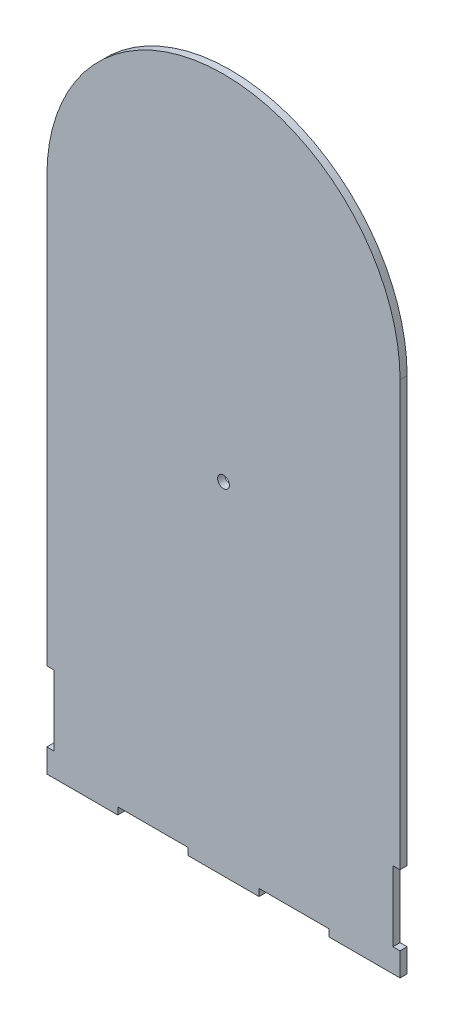
SolidWorks part; units mm, degrees
ref_plane "Front Plane" through (0, 0, 0) normal (0, 0, 1) x (1, 0, 0)
ref_plane "Top Plane" through (0, 0, 0) normal (0, 1, 0) x (1, 0, 0)
ref_plane "Right Plane" through (0, 0, 0) normal (1, 0, 0) x (0, 0, -1)
sketch "Sketch1" plane through (0, 0, 0) normal (0, 0, 1) x (1, 0, 0)
  line L0 (90.1, 0) -> (90.1, 3)
  line L1 (0, 0) -> (150, 0)
  line L2 (0, 0) -> (0, 220)
  line L3 (0, 220) -> (150, 220)
  line L4 (150, 0) -> (150, 220)
  line L5 (150, 39.8) -> (147, 39.8)
  line L6 (150, 39.8) -> (150, 10)
  line L7 (150, 10) -> (147, 10)
  line L8 (147, 39.8) -> (147, 10)
  line L9 (30.1, 0) -> (59.9, 0)
  line L10 (30.1, 0) -> (30.1, 3)
  line L11 (30.1, 3) -> (59.9, 3)
  line L12 (59.9, 0) -> (59.9, 3)
  line L13 (90.1, 0) -> (119.9, 0)
  line L14 (119.9, 0) -> (119.9, 3)
  line L15 (90.1, 3) -> (119.9, 3)
  line L16 (75, -730) -> (75, 49270) construction
  line L17 (0, 10) -> (3, 10)
  line L18 (3, 39.8) -> (3, 10)
  line L19 (0, 39.8) -> (3, 39.8)
  line L20 (0, 39.8) -> (0, 10)
  circle A0 centre (75, 220) radius 75
  circle A1 centre (75, 145) radius 2.5
  dimension "D11" = 5
  dimension "D1" = 220
  dimension "D2" = 150
  dimension "D3" = 3
  dimension "D4" = 10
  dimension "D5" = 29.8
  dimension "D6" = 3
  dimension "D7" = 29.8
  dimension "D8" = 30.1
  dimension "D10" = 30.2
  dimension "D9" = 2
extrude "Boss-Extrude1" add sketch "Sketch1" along normal blind 3 contours L1 L16 A0 L2 L19 L18 L17 L10 L11 L12 | L16 L1 L0 L15 L14 L4 L7 L8 L5 A0 | L16 L3 A0 | L16 A0 L3 | A0 L16 L3 | L3 L16 A0
